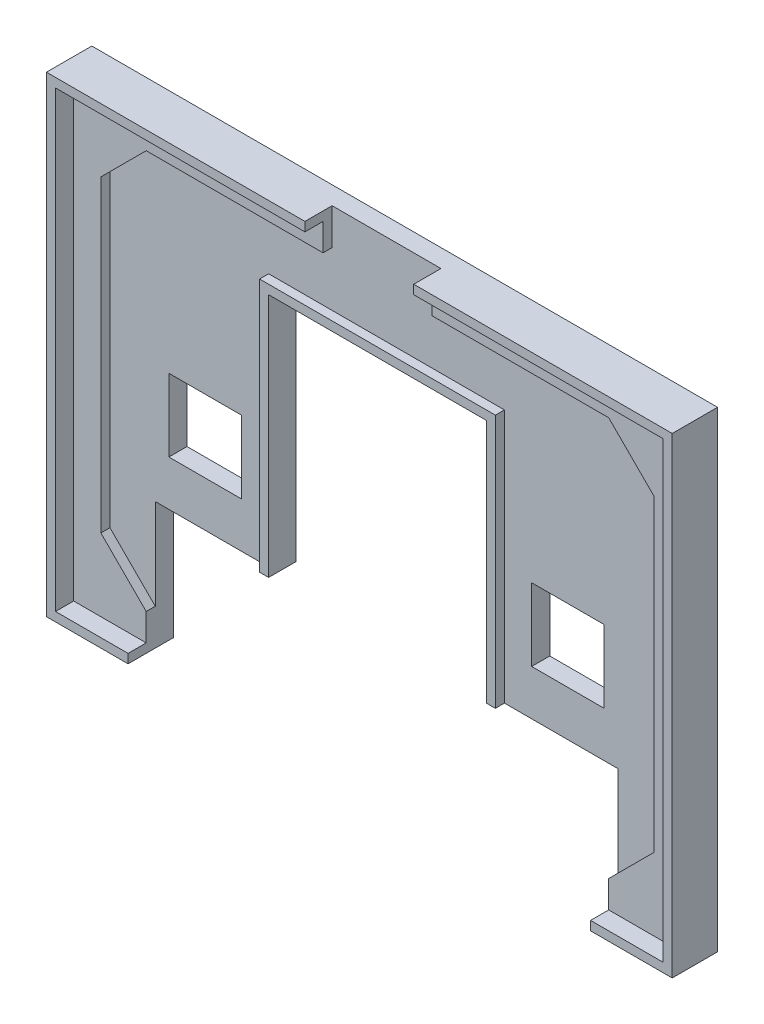
SolidWorks part; units mm, degrees
ref_plane "Přední rovina" through (0, 0, 0) normal (0, 0, 1) x (1, 0, 0)
ref_plane "Horní rovina" through (0, 0, 0) normal (0, 1, 0) x (1, 0, 0)
ref_plane "Pravá rovina" through (0, 0, 0) normal (1, 0, 0) x (0, 0, -1)
sketch "Skica1" plane through (0, 0, 0) normal (0, 0, 1) x (1, 0, 0)
  line L1 (-33.5, -25) -> (33.5, -25)
  line L2 (-33.5, -25) -> (-33.5, 25)
  line L3 (-33.5, 25) -> (33.5, 25)
  line L4 (33.5, -25) -> (33.5, 25)
  line L5 (-33.5, -25) -> (33.5, 25) construction
  line L6 (-33.5, 25) -> (33.5, -25) construction
  point P0 (0, 0)
  dimension "D1" = 67
  dimension "D2" = 50
extrude "Přidat vysunutím1" add sketch "Skica1" along normal blind 3
sketch "Skica2" plane through (0, 0, 3) normal (0, 0, 1) x (1, 0, 0)
  line L0 (-1000, 0) -> (49000, 0) construction
  line L1 (0, -1000) -> (0, 49000) construction
  line L2 (-1000, -22) -> (49000, -22) construction
  line L3 (-25.5, -1000) -> (-25.5, 49000) construction
  line L4 (-30.5, -1000) -> (-30.5, 49000) construction
  line L6 (-33.5, -25) -> (33.5, -25) construction
  line L7 (-25.5, -22) -> (-30.5, -17)
  line L8 (-30.5, -17) -> (-30.5, 17)
  line L9 (-25.5, -22) -> (25.5, -22)
  line L10 (30.5, -17) -> (30.5, 17)
  line L11 (25.5, -22) -> (30.5, -17)
  line L12 (25.5, 22) -> (30.5, 17)
  line L13 (-25.5, 22) -> (25.5, 22)
  line L14 (-25.5, 22) -> (-30.5, 17)
  point P20 (0, -22)
  point P21 (30.5, 0)
  point P24 (-30.5, 0)
  dimension "D1" = 30.5
  dimension "D2" = 5
  dimension "D3" = 3
  dimension "D4" = 45
extrude "Odebrat vysunutím1" cut sketch "Skica2" against normal offset from surface (1 mm away) 2 up to face at (0, 0, 0)
sketch "Skica3" plane through (0, 0, 0) normal (0, 0, -1) x (-1, 0, 0)
  line L0 (0, -1000) -> (0, 49000) construction
  line L1 (33.5, -25) -> (-33.5, -25) construction
  line L2 (24, 1) -> (16, 1)
  line L3 (24, 1) -> (24, -7)
  line L4 (24, -7) -> (16, -7)
  line L5 (16, 1) -> (16, -7)
  line L6 (-16, 1) -> (-16, -7)
  line L7 (33.5, -25) -> (-33.5, -25) construction
  line L8 (25.5, -25) -> (-25.5, -25)
  line L9 (25.5, -25) -> (25.5, -12)
  line L11 (-25.5, -25) -> (-25.5, -12)
  line L12 (-24, -7) -> (-16, -7)
  line L13 (25.5, -12) -> (12, -12)
  line L15 (12, -12) -> (12, 15)
  line L16 (12, 15) -> (-12, 15)
  line L17 (-12, -12) -> (-12, 15)
  line L18 (-12, -12) -> (-25.5, -12)
  line L19 (-24, 1) -> (-24, -7)
  line L20 (-24, 1) -> (-16, 1)
  dimension "D1" = 16
  dimension "D2" = 8
  dimension "D3" = 18
  dimension "D4" = 13
  dimension "D5" = 51
  dimension "D6" = 24
  dimension "D7" = 27
extrude "Odebrat vysunutím2" cut sketch "Skica3" against normal through all
sketch "Skica4" plane through (0, 0, 2) normal (0, 0, 1) x (1, 0, 0)
  line L0 (12, 15) -> (12, -12) construction
  line L1 (-12, -12) -> (-12, 15) construction
  line L2 (-12, 15) -> (12, 15) construction
  line L3 (12, 15) -> (12, -12)
  line L4 (-12, -12) -> (-12, 15)
  line L5 (-12, 15) -> (12, 15)
extrude "Vysunout tenkostěnný1" add sketch "Skica4" along normal up to surface (1 mm away) thin up to face at (0, -3.5714, 3) thin type one direction reverse wall 1
sketch "Skica5" plane through (0, 0, 0) normal (0, 0, -1) x (-1, 0, 0)
  line L0 (-33.5, 25) -> (33.5, 25) construction
  line L1 (33.5, 25) -> (33.5, -25) construction
  line L2 (33.5, -25) -> (25.5, -25) construction
  line L3 (-33.5, -25) -> (-33.5, 25) construction
  line L4 (-25.5, -25) -> (-33.5, -25) construction
  line L5 (-33.5, 25) -> (33.5, 25)
  line L6 (33.5, 25) -> (33.5, -25)
  line L7 (33.5, -25) -> (25.5, -25)
  line L8 (-33.5, -25) -> (-33.5, 25)
  line L9 (-25.5, -25) -> (-33.5, -25)
extrude "Vysunout tenkostěnný2" add sketch "Skica5" against normal blind 5 thin thin type one direction reverse wall 1
sketch "Skica6" plane through (0, 0, 2) normal (0, 0, 1) x (1, 0, 0)
  line L0 (0, -1000) -> (0, 49000) construction
  line L1 (25.5, 22) -> (-25.5, 22) construction
  line L2 (-6, 22) -> (6, 22)
  line L3 (-6, 22) -> (-6, 26)
  line L4 (-6, 26) -> (6, 26)
  line L5 (6, 22) -> (6, 26)
  line L6 (34.5, 26) -> (-34.5, 26) construction
  dimension "D1" = 12
extrude "Odebrat vysunutím3" cut sketch "Skica6" along normal through all
sketch "Skica7" plane through (0, 0, 0) normal (0, 0, -1) x (-1, 0, 0)
  line L0 (-29.2572, 22.893) -> (-26.612, 22.893)
  line L1 (-26.612, 22.893) -> (-26.612, 21.8489)
  line L2 (-26.612, 21.8489) -> (-25.3358, 21.8489)
  line L3 (-25.3358, 21.8489) -> (-25.3358, 17.0458)
  line L4 (-25.3358, 17.0458) -> (-26.612, 17.0458)
  line L5 (-26.612, 17.0458) -> (-26.612, 15.9552)
  line L6 (-26.612, 15.9552) -> (-29.2572, 15.9552)
  line L7 (-29.2572, 15.9552) -> (-29.2572, 17.0458)
  line L8 (-29.2572, 17.0458) -> (-30.603, 17.0458)
  line L9 (-30.603, 17.0458) -> (-30.603, 20.5959)
  line L10 (-30.603, 20.5959) -> (-29.2572, 20.5959)
  line L11 (-29.2572, 20.5959) -> (-29.2572, 22.893)
  line L12 (-19.9527, 22.893) -> (-21.2521, 22.893)
  line L13 (-21.2521, 22.893) -> (-21.2521, 21.8489)
  line L14 (-21.2521, 21.8489) -> (-22.5514, 21.8489)
  line L15 (-22.5514, 21.8489) -> (-22.5514, 17.0458)
  line L16 (-22.5514, 17.0458) -> (-21.2521, 17.0458)
  line L17 (-21.2521, 17.0458) -> (-21.2521, 15.9552)
  line L18 (-21.2521, 15.9552) -> (-15.9385, 15.9552)
  line L19 (-15.9385, 15.9552) -> (-15.9385, 18.0435)
  line L20 (-15.9385, 18.0435) -> (-17.1915, 18.0435)
  line L21 (-17.1915, 18.0435) -> (-17.1915, 20.5959)
  line L22 (-17.1915, 20.5959) -> (-18.5953, 20.5959)
  line L23 (-18.5953, 20.5959) -> (-18.5953, 21.8489)
  line L24 (-18.5953, 21.8489) -> (-19.9527, 21.8489)
  line L25 (-19.9527, 21.8489) -> (-19.9527, 22.893)
  line L26 (-30.603, 14.4934) -> (-29.2572, 14.4934)
  line L27 (-29.2572, 14.4934) -> (-29.2572, 13.4029)
  line L28 (-29.2572, 13.4029) -> (-27.9346, 13.4029)
  line L29 (-27.9346, 13.4029) -> (-27.9346, 14.4934)
  line L30 (-27.9346, 14.4934) -> (-26.612, 14.4934)
  line L31 (-26.612, 14.4934) -> (-26.612, 13.4029)
  line L32 (-26.612, 13.4029) -> (-23.9204, 13.4029)
  line L33 (-23.9204, 13.4029) -> (-23.9204, 14.4934)
  line L34 (-23.9204, 14.4934) -> (-22.5514, 14.4934)
  line L35 (-22.5514, 14.4934) -> (-22.5514, 13.4029)
  line L36 (-22.5514, 13.4029) -> (-19.9527, 13.4029)
  line L37 (-19.9527, 13.4029) -> (-19.9527, 14.4934)
  line L38 (-19.9527, 14.4934) -> (-18.5953, 14.4934)
  line L39 (-18.5953, 14.4934) -> (-18.5953, 13.4029)
  line L40 (-18.5953, 13.4029) -> (-17.1915, 13.4029)
  line L41 (-17.1915, 13.4029) -> (-17.1915, 14.4934)
  line L42 (-17.1915, 14.4934) -> (-15.9385, 14.4934)
  line L43 (-15.9385, 14.4934) -> (-15.9385, 12.2427)
  line L44 (-15.9385, 12.2427) -> (-14.5927, 12.2427)
  line L45 (-14.5927, 12.2427) -> (-14.5927, 9.6439)
  line L46 (-14.5927, 9.6439) -> (-17.1915, 9.6439)
  line L47 (-17.1915, 9.6439) -> (-17.1915, 10.9433)
  line L48 (-17.1915, 10.9433) -> (-18.5953, 10.9433)
  line L49 (-18.5953, 10.9433) -> (-18.5953, 8.623)
  line L50 (-18.5953, 8.623) -> (-19.9527, 8.623)
  line L51 (-19.9527, 8.623) -> (-19.9527, 9.7832)
  line L52 (-19.9527, 9.7832) -> (-22.5514, 9.7832)
  line L53 (-22.5514, 9.7832) -> (-22.5514, 10.9433)
  line L54 (-22.5514, 10.9433) -> (-23.9204, 10.9433)
  line L55 (-23.9204, 10.9433) -> (-23.9204, 9.7832)
  line L57 (-25.2662, 9.6439) -> (-25.2662, 8.623)
  line L58 (-25.2662, 8.623) -> (-26.612, 8.623)
  line L59 (-26.612, 8.623) -> (-26.612, 10.9433)
  line L60 (-26.612, 10.9433) -> (-27.9346, 10.9433)
  line L61 (-27.9346, 10.9433) -> (-27.9346, 9.6439)
  line L62 (-27.9346, 9.6439) -> (-29.2572, 9.6439)
  line L64 (-29.3964, 8.623) -> (-30.603, 8.623)
  line L65 (-30.603, 8.623) -> (-30.603, 10.9433)
  line L66 (-30.603, 10.9433) -> (-31.972, 10.9433)
  line L67 (-31.972, 10.9433) -> (-31.972, 13.4029)
  line L68 (-31.972, 13.4029) -> (-30.603, 13.4029)
  line L69 (-30.603, 13.4029) -> (-30.603, 14.4934)
  line L70 (-29.3964, 8.623) -> (-29.3964, 9.6439)
  line L71 (-29.3964, 9.6439) -> (-29.2572, 9.6439)
  line L72 (-23.9204, 9.7832) -> (-25.2662, 9.7832)
  line L73 (-25.2662, 9.7832) -> (-25.2662, 9.6439)
  line L74 (34.5, 26) -> (34.5, -26) construction
  line L75 (34.5, -26) -> (25.5, -26) construction
  line L76 (0, 0) -> (0, 37.9765) construction
  line L77 (23.9204, 9.7832) -> (25.2662, 9.7832)
  line L78 (23.9204, 10.9433) -> (23.9204, 9.7832)
  line L79 (22.5514, 10.9433) -> (23.9204, 10.9433)
  line L80 (22.5514, 9.7832) -> (22.5514, 10.9433)
  line L81 (19.9527, 9.7832) -> (22.5514, 9.7832)
  line L82 (19.9527, 8.623) -> (19.9527, 9.7832)
  line L83 (18.5953, 8.623) -> (19.9527, 8.623)
  line L84 (18.5953, 10.9433) -> (18.5953, 8.623)
  line L85 (17.1915, 10.9433) -> (18.5953, 10.9433)
  line L86 (17.1915, 9.6439) -> (17.1915, 10.9433)
  line L87 (14.5927, 9.6439) -> (17.1915, 9.6439)
  line L88 (14.5927, 12.2427) -> (14.5927, 9.6439)
  line L89 (15.9385, 12.2427) -> (14.5927, 12.2427)
  line L90 (15.9385, 14.4934) -> (15.9385, 12.2427)
  line L91 (17.1915, 14.4934) -> (15.9385, 14.4934)
  line L92 (17.1915, 13.4029) -> (17.1915, 14.4934)
  line L93 (18.5953, 13.4029) -> (17.1915, 13.4029)
  line L94 (18.5953, 14.4934) -> (18.5953, 13.4029)
  line L95 (19.9527, 14.4934) -> (18.5953, 14.4934)
  line L96 (19.9527, 13.4029) -> (19.9527, 14.4934)
  line L97 (22.5514, 13.4029) -> (19.9527, 13.4029)
  line L98 (22.5514, 14.4934) -> (22.5514, 13.4029)
  line L99 (23.9204, 14.4934) -> (22.5514, 14.4934)
  line L100 (23.9204, 13.4029) -> (23.9204, 14.4934)
  line L101 (26.612, 13.4029) -> (23.9204, 13.4029)
  line L102 (26.612, 14.4934) -> (26.612, 13.4029)
  line L103 (27.9346, 14.4934) -> (26.612, 14.4934)
  line L104 (27.9346, 13.4029) -> (27.9346, 14.4934)
  line L105 (29.2572, 13.4029) -> (27.9346, 13.4029)
  line L106 (29.2572, 14.4934) -> (29.2572, 13.4029)
  line L107 (30.603, 14.4934) -> (29.2572, 14.4934)
  line L108 (30.603, 13.4029) -> (30.603, 14.4934)
  line L109 (31.972, 13.4029) -> (30.603, 13.4029)
  line L110 (31.972, 10.9433) -> (31.972, 13.4029)
  line L111 (30.603, 10.9433) -> (31.972, 10.9433)
  line L112 (30.603, 8.623) -> (30.603, 10.9433)
  line L113 (29.3964, 8.623) -> (30.603, 8.623)
  line L114 (29.3964, 8.623) -> (29.3964, 9.6439)
  line L115 (29.3964, 9.6439) -> (29.2572, 9.6439)
  line L116 (27.9346, 9.6439) -> (29.2572, 9.6439)
  line L117 (27.9346, 10.9433) -> (27.9346, 9.6439)
  line L118 (26.612, 10.9433) -> (27.9346, 10.9433)
  line L119 (26.612, 8.623) -> (26.612, 10.9433)
  line L120 (25.2662, 8.623) -> (26.612, 8.623)
  line L121 (25.2662, 9.6439) -> (25.2662, 8.623)
  line L122 (25.2662, 9.7832) -> (25.2662, 9.6439)
  line L123 (18.5953, 21.8489) -> (19.9527, 21.8489)
  line L124 (18.5953, 20.5959) -> (18.5953, 21.8489)
  line L125 (17.1915, 20.5959) -> (18.5953, 20.5959)
  line L126 (17.1915, 18.0435) -> (17.1915, 20.5959)
  line L127 (15.9385, 18.0435) -> (17.1915, 18.0435)
  line L128 (15.9385, 15.9552) -> (15.9385, 18.0435)
  line L129 (21.2521, 15.9552) -> (15.9385, 15.9552)
  line L130 (21.2521, 17.0458) -> (21.2521, 15.9552)
  line L131 (22.5514, 17.0458) -> (21.2521, 17.0458)
  line L132 (22.5514, 21.8489) -> (22.5514, 17.0458)
  line L133 (21.2521, 21.8489) -> (22.5514, 21.8489)
  line L134 (21.2521, 22.893) -> (21.2521, 21.8489)
  line L135 (19.9527, 22.893) -> (21.2521, 22.893)
  line L136 (19.9527, 21.8489) -> (19.9527, 22.893)
  line L137 (30.603, 20.5959) -> (29.2572, 20.5959)
  line L138 (30.603, 17.0458) -> (30.603, 20.5959)
  line L139 (29.2572, 17.0458) -> (30.603, 17.0458)
  line L140 (29.2572, 15.9552) -> (29.2572, 17.0458)
  line L141 (26.612, 15.9552) -> (29.2572, 15.9552)
  line L142 (26.612, 17.0458) -> (26.612, 15.9552)
  line L143 (25.3358, 17.0458) -> (26.612, 17.0458)
  line L144 (25.3358, 21.8489) -> (25.3358, 17.0458)
  line L145 (26.612, 21.8489) -> (25.3358, 21.8489)
  line L146 (26.612, 22.893) -> (26.612, 21.8489)
  line L147 (29.2572, 22.893) -> (26.612, 22.893)
  line L148 (29.2572, 20.5959) -> (29.2572, 22.893)
  dimension "D1" = 49.0927
  dimension "D2" = 50.4385
  dimension "D3" = 51.6915
  dimension "D4" = 53.0953
  dimension "D5" = 54.4527
  dimension "D6" = 58.4204
  dimension "D7" = 59.8358
  dimension "D8" = 62.4346
  dimension "D9" = 34.623
  dimension "D10" = 35.6439
  dimension "D11" = 39.4029
  dimension "D12" = 40.4934
  dimension "D13" = 41.9552
  dimension "D14" = 46.5959
  dimension "D15" = 48.893
  dimension "D18" = 44.0435
extrude "Odebrat vysunutím4" cut sketch "Skica7" against normal blind 1
sketch "Skica8" plane through (0, 0, 0) normal (0, 0, -1) x (-1, 0, 0)
  line L0 (-31.972, 13.4029) -> (-31.972, 10.9433) construction
  line L1 (-30.603, 8.623) -> (-29.3964, 8.623) construction
  text T0 "PUMP" font "BLOXAT" height 5.8
  dimension "D1" = 20.7027
  dimension "D2" = 8.868
extrude "Odebrat vysunutím5" cut sketch "Skica8" against normal blind 1
